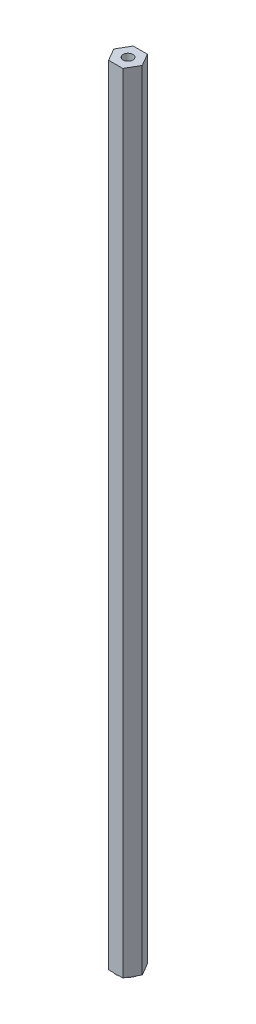
SolidWorks part; units mm, degrees
material "6063-T6"
ref_plane "Front" through (0, 0, 0) normal (0, 0, 1) x (1, 0, 0)
ref_plane "Top" through (0, 0, 0) normal (0, 1, 0) x (1, 0, 0)
ref_plane "Right" through (0, 0, 0) normal (1, 0, 0) x (0, 0, -1)
sketch "Sketch1" plane through (0, 0, 0) normal (0, 1, 0) x (1, 0, 0)
  line L1 (7.3323, 0) -> (3.6662, 6.35)
  line L2 (3.6662, 6.35) -> (-3.6662, 6.35)
  line L3 (-3.6662, 6.35) -> (-7.3323, 0)
  line L4 (-7.3323, 0) -> (-3.6662, -6.35)
  line L5 (-3.6662, -6.35) -> (3.6662, -6.35)
  line L6 (3.6662, -6.35) -> (7.3323, 0)
  circle A0 centre (0, 0) radius 6.35 construction
extrude "Boss-Extrude1" add sketch "Sketch1" along normal blind 406.4
sketch "Sketch2" plane through (0, 406.4, 0) normal (0, 1, 0) x (1, 0, 0)
  circle A0 centre (0, 0) radius 2.54
  dimension "D1" = 5.08
extrude "Cut-Extrude1" cut sketch "Sketch2" against normal blind 25.4
sketch "Sketch3" plane through (0, 0, 0) normal (0, -1, 0) x (1, 0, 0)
  circle A0 centre (0, 0) radius 6.35
extrude "Boss-Extrude2" add sketch "Sketch3" along normal blind 0.254
